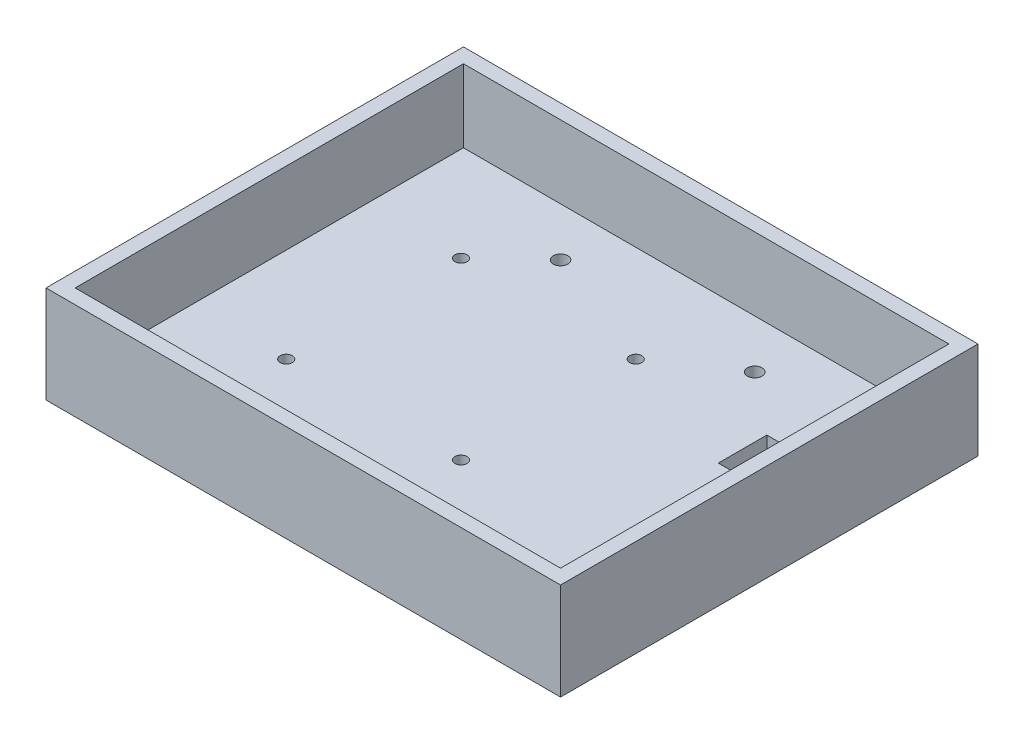
SolidWorks part; units mm, degrees
material "ABS PC"
ref_plane "前视基准面" through (0, 0, 0) normal (0, 0, 1) x (1, 0, 0)
ref_plane "上视基准面" through (0, 0, 0) normal (0, 1, 0) x (1, 0, 0)
ref_plane "右视基准面" through (0, 0, 0) normal (1, 0, 0) x (0, 0, -1)
sketch "草图1" plane through (0, 0, 0) normal (0, 1, 0) x (1, 0, 0)
  line L1 (-50, 40) -> (50, 40)
  line L2 (-50, 40) -> (-50, -40)
  line L3 (-50, -40) -> (50, -40)
  line L4 (50, 40) -> (50, -40)
  line L5 (-50, 40) -> (50, -40) construction
  line L6 (-50, -40) -> (50, 40) construction
  point P0 (0, 0)
extrude "凸台-拉伸1" add sketch "草图1" along normal blind 5
sketch "草图2" plane through (0, 5, 0) normal (0, 1, 0) x (1, 0, 0)
  circle A0 centre (20, 30) radius 1.5
sketch "草图3" plane through (0, 5, 0) normal (0, 1, 0) x (1, 0, 0)
  line L0 (0, 40) -> (0, -40) construction
  line L1 (50, 40) -> (-50, 40) construction
  line L2 (-50, -40) -> (50, -40) construction
  line L3 (-50, 0) -> (50, 0) construction
  line L4 (-50, 40) -> (-50, -40) construction
  line L5 (50, -40) -> (50, 40) construction
ref_plane "基准面1" through (0, 0, 0) normal (-1, 0, 0) x (0, 0, 1)
ref_plane "基准面2" through (0, 0, 0) normal (0, 0, 1) x (1, 0, 0)
extrude "切除-拉伸1" cut sketch "草图2" against normal through all contours A0
mirror "镜向1" about plane through (0, 0, 0) normal (-1, 0, 0) of "切除-拉伸1"
mirror "镜向2" about plane through (0, 0, 0) normal (0, 0, 1) of "镜向1", "切除-拉伸1"
sketch "草图4" plane through (0, 0, 40) normal (0, 0, 1) x (1, 0, 0)
  line L0 (-50, 0) -> (-50, 20)
  line L1 (-50, 20) -> (50, 20)
  line L2 (50, 20) -> (50, 0)
  line L3 (50, 0) -> (-50, 0)
extrude "凸台-拉伸2" add sketch "草图4" along normal blind 3
sketch "草图5" plane through (-50, 0, 0) normal (-1, 0, 0) x (0, 0, 1)
  line L0 (-40, 0) -> (-40, 20)
  line L1 (-40, 5) -> (-40, 0) construction
  line L2 (-40, 20) -> (43, 20)
  line L3 (43, 20) -> (43, 0)
  line L4 (43, 0) -> (-40, 0)
extrude "凸台-拉伸3" add sketch "草图5" along normal blind 3
mirror "镜向3" about plane through (0, 0, 0) normal (-1, 0, 0) of "凸台-拉伸3"
sketch "草图6" plane through (0, 0, -40) normal (0, 0, -1) x (-1, 0, 0)
  line L0 (-53, 20) -> (53, 20)
  line L1 (53, 20) -> (53, 0)
  line L2 (53, 0) -> (-53, 0)
  line L3 (-53, 0) -> (-53, 20)
extrude "凸台-拉伸4" add sketch "草图6" along normal blind 3
sketch "草图7" plane through (0, 5, 0) normal (0, 1, 0) x (1, 0, 0)
  line L0 (5.45, 20.04) -> (-30.55, 20.04)
  line L1 (-30.55, 20.04) -> (-30.55, -15.96)
  line L2 (-30.55, -15.96) -> (5.45, -15.96)
  circle A0 centre (5.45, 20.04) radius 1.25
  circle A2 centre (-30.55, 20.04) radius 1.25
  circle A3 centre (-30.55, -15.96) radius 1.25
  circle A4 centre (5.45, -15.96) radius 1.25
extrude "切除-拉伸2" cut sketch "草图7" against normal through all contours A2 | A0 | A4 | A3
sketch "草图8" plane through (0, 0, 0) normal (0, -1, 0) x (1, 0, 0)
  line L0 (0, -40) -> (0, 40) construction
  line L1 (-28.0112, 17.4258) -> (-30.55, 18.8915)
  line L2 (-30.55, 18.8915) -> (-33.0888, 17.4258)
  line L3 (-33.0888, 17.4258) -> (-33.0888, 14.4942)
  line L4 (-33.0888, 14.4942) -> (-30.55, 13.0285)
  line L5 (-30.55, 13.0285) -> (-28.0112, 14.4942)
  line L6 (-28.0112, 14.4942) -> (-28.0112, 17.4258)
  line L8 (-30.55, -17.0378) -> (-33.15, -18.5389)
  line L9 (-33.15, -18.5389) -> (-33.15, -21.5411)
  line L10 (-33.15, -21.5411) -> (-30.55, -23.0422)
  line L11 (-30.55, -23.0422) -> (-27.95, -21.5411)
  line L12 (-27.95, -21.5411) -> (-27.95, -18.5389)
  line L13 (-27.95, -18.5389) -> (-30.55, -17.0378)
  line L14 (5.45, 18.9622) -> (2.85, 17.4611)
  line L15 (2.85, 17.4611) -> (2.85, 14.4589)
  line L16 (2.85, 14.4589) -> (5.45, 12.9578)
  line L17 (5.45, 12.9578) -> (8.05, 14.4589)
  line L18 (8.05, 14.4589) -> (8.05, 17.4611)
  line L19 (8.05, 17.4611) -> (5.45, 18.9622)
  line L20 (5.45, -17.0378) -> (2.85, -18.5389)
  line L21 (2.85, -18.5389) -> (2.85, -21.5411)
  line L22 (2.85, -21.5411) -> (5.45, -23.0422)
  line L23 (5.45, -23.0422) -> (8.05, -21.5411)
  line L24 (8.05, -21.5411) -> (8.05, -18.5389)
  line L25 (8.05, -18.5389) -> (5.45, -17.0378)
  circle A0 centre (-30.55, 15.96) radius 2.5388 construction
  circle A1 centre (-30.55, -20.04) radius 2.6 construction
  circle A2 centre (5.45, 15.96) radius 2.6 construction
  circle A3 centre (5.45, -20.04) radius 2.6 construction
extrude "切除-拉伸3" cut sketch "草图8" against normal blind 2 contours L6 L1 L2 L3 L4 L5 | L13 L8 L9 L10 L11 L12 | L25 L20 L21 L22 L23 L24 | L19 L14 L15 L16 L17 L18
sketch "草图9" plane through (0, 5, 0) normal (0, 1, 0) x (1, 0, 0)
  line L1 (32.5, 20) -> (47.5, 20)
  line L2 (32.5, 20) -> (32.5, 10)
  line L3 (32.5, 10) -> (47.5, 10)
  line L4 (47.5, 20) -> (47.5, 10)
  line L5 (32.5, 20) -> (47.5, 10) construction
  line L6 (32.5, 10) -> (47.5, 20) construction
  point P0 (40, 15)
  point P5 (0, 0)
  point P6 (0, 0)
extrude "切除-拉伸4" cut sketch "草图9" against normal through all
